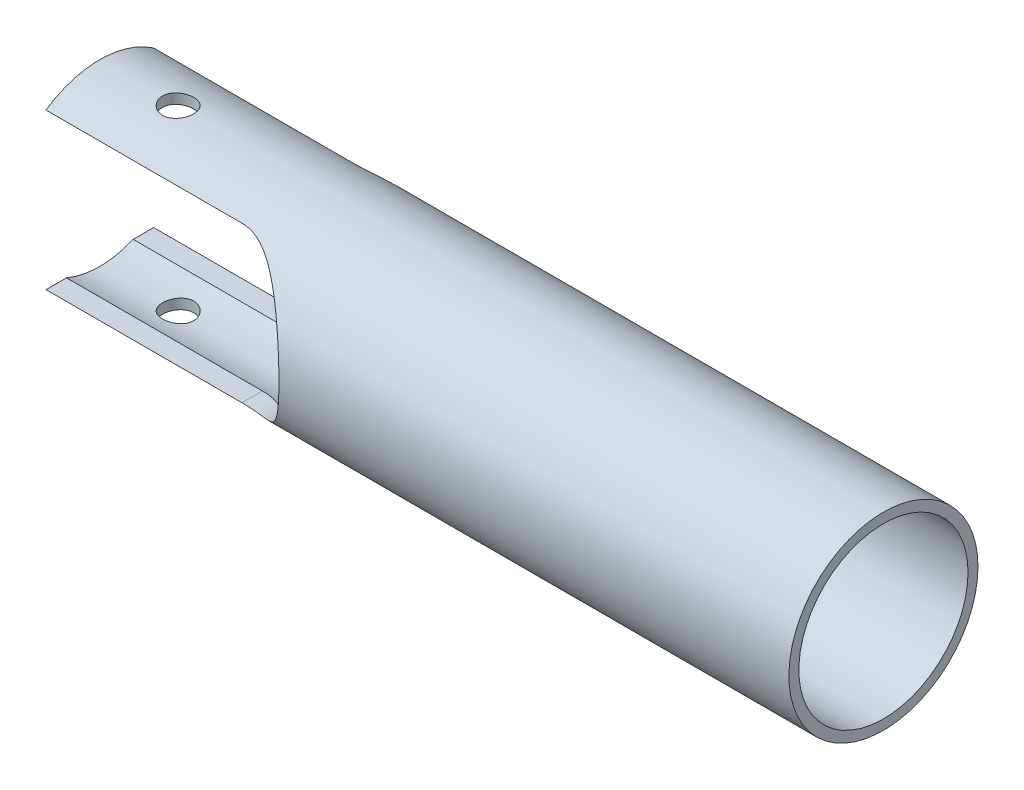
SolidWorks part; units mm, degrees
ref_plane "Front Plane" through (0, 0, 0) normal (0, 0, 1) x (1, 0, 0)
ref_plane "Top Plane" through (0, 0, 0) normal (0, 1, 0) x (1, 0, 0)
ref_plane "Right Plane" through (0, 0, 0) normal (1, 0, 0) x (0, 0, -1)
sketch "Sketch1" plane through (0, 0, 0) normal (1, 0, 0) x (0, 0, -1)
  circle A0 centre (0, 0) radius 1.0795
  circle A1 centre (0, 0) radius 1.2065
  dimension "D1" = 2.413
  dimension "D2" = 2.159
extrude "Boss-Extrude1" add sketch "Sketch1" along normal blind 10
sketch "Sketch2" plane through (0, 0, 0) normal (0, 0, 1) x (1, 0, 0)
  line L0 (0, 1.2065) -> (0, -1.2065) construction
  line L1 (0, 1.2065) -> (0, -1.2065) construction
  line L2 (2.5, -0.9922) -> (0, -0.9922)
  line L3 (0, -0.9922) -> (0, 0.9922)
  line L4 (0, 0.9922) -> (2.5, 0.9922)
  circle A1 centre (2.5, 0) radius 0.9922 construction
  arc A2 (2.5, -0.9922) -> (2.5, 0.9922) centre (2.5, 0) ccw
  dimension "D1" = 1.9844
  dimension "D2" = 2.5
extrude "Cut-Extrude1" cut sketch "Sketch2" against normal blind 1.5 and the other way blind 10
sketch "Sketch4" plane through (0, 0, 0) normal (0, 1, 0) x (1, 0, 0)
  line L1 (0, 0.4253) -> (0, -0.4253) construction
  line L2 (-1, 0) -> (1, 0) construction
  line L5 (0, 0.4253) -> (0, -0.4253) construction
  circle A0 centre (1, 0) radius 0.1984
  dimension "D1" = 0.3969
  dimension "D2" = 1
extrude "Cut-Extrude2" cut sketch "Sketch4" against normal blind 5 and the other way blind 5
equation "\"pin_hole_position\"=1.5"
equation "\"D2@Sketch4\"=\"pin_hole_position\" - 0.5"
equation "\"D2@Sketch2\"=\"pin_hole_position\"+1"
